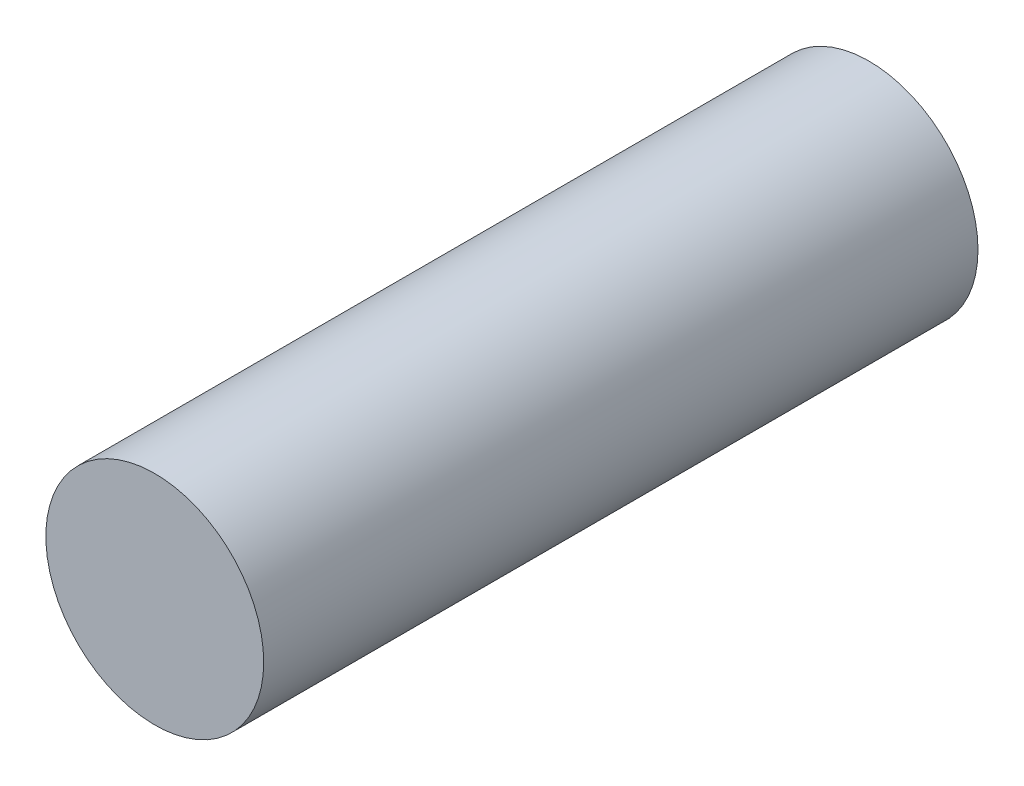
SolidWorks part; units mm, degrees
material "Ceramic Porcelain"
ref_plane "Front Plane" through (0, 0, 0) normal (0, 0, 1) x (1, 0, 0)
ref_plane "Top Plane" through (0, 0, 0) normal (0, 1, 0) x (1, 0, 0)
ref_plane "Right Plane" through (0, 0, 0) normal (1, 0, 0) x (0, 0, -1)
sketch "Sketch1" plane through (0, 0, 0) normal (0, 0, 1) x (1, 0, 0)
  circle A0 centre (0, 0) radius 3.05
  dimension "D1" = 6.1
extrude "Boss-Extrude1" add sketch "Sketch1" along normal blind 3 and the other way blind 17 contours A0
